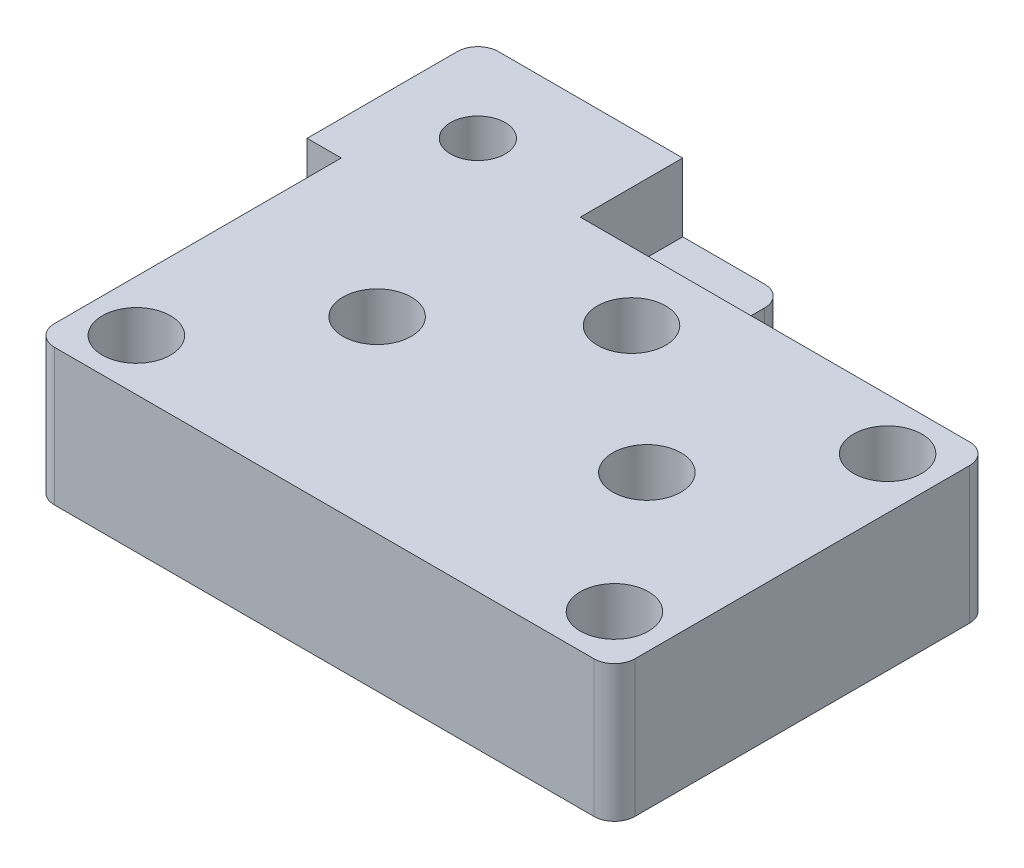
SolidWorks part; units mm, degrees
ref_plane "Alzado" through (0, 0, 0) normal (0, 0, 1) x (1, 0, 0)
ref_plane "Planta" through (0, 0, 0) normal (0, 1, 0) x (1, 0, 0)
ref_plane "Vista lateral" through (0, 0, 0) normal (1, 0, 0) x (0, 0, -1)
sketch "Croquis1" plane through (0, 0, 0) normal (0, 1, 0) x (1, 0, 0)
  line L0 (-2.5, 27.5) -> (-2.5, 42.5)
  line L1 (-42.5, -27.5) -> (42.5, -27.5)
  line L2 (-42.5, -27.5) -> (-42.5, 17.5)
  line L3 (-2.5, 27.5) -> (42.5, 27.5)
  line L4 (42.5, -27.5) -> (42.5, 27.5)
  line L5 (-42.5, -27.5) -> (42.5, 27.5) construction
  line L6 (0, 0) -> (42.5, -27.5) construction
  line L7 (-2.5, 42.5) -> (-47.5, 42.5)
  line L8 (-47.5, 42.5) -> (-47.5, 17.5)
  line L9 (-47.5, 17.5) -> (-42.5, 17.5)
  point P0 (0, 0)
  dimension "D1" = 85
  dimension "D2" = 55
  dimension "D3" = 5
  dimension "D4" = 25
  dimension "D5" = 45
  dimension "D6" = 15
  dimension "D7" = 27.5
extrude "Saliente-Extruir1" add sketch "Croquis1" along normal blind 20
sketch "Croquis2" plane through (0, 20, 0) normal (0, 1, 0) x (1, 0, 0)
  line L0 (-19.75, 0) -> (19.75, 0) construction
  line L1 (42.5, 20) -> (-35, 20) construction
  line L2 (42.5, -27.5) -> (42.5, 27.5) construction
  line L3 (-35, 20) -> (-35, -20) construction
  line L4 (-35, -20) -> (35, -20) construction
  line L5 (35, -20) -> (35, 20) construction
  line L6 (42.5, 27.5) -> (-2.5, 27.5) construction
  line L7 (-42.5, -27.5) -> (42.5, -27.5) construction
  line L8 (-42.5, 17.5) -> (-42.5, -27.5) construction
  line L9 (-2.5, 27.5) -> (-2.5, 42.5) construction
  line L10 (-2.5, 42.5) -> (-47.5, 42.5) construction
  circle A0 centre (-19.75, 0) radius 20 construction
  circle A1 centre (19.75, 0) radius 20 construction
  circle A2 centre (35, 20) radius 2.5
  circle A3 centre (35, -20) radius 2.5
  circle A4 centre (-35, -20) radius 2.5
  circle A5 centre (-10, 35) radius 2.5
  circle A7 centre (-19.75, 0) radius 5
  circle A8 centre (19.75, 0) radius 5
  point P5 (0, 0)
  dimension "D1" = 40
  dimension "D2" = 40
  dimension "D4" = 5
  dimension "D11" = 10
  dimension "D12" = 10
  dimension "D3" = 39.5
  dimension "D5" = 7.5
  dimension "D6" = 7.5
  dimension "D7" = 7.5
  dimension "D8" = 7.5
  dimension "D9" = 7.5
  dimension "D10" = 7.5
extrude "Cortar-Extruir1" cut sketch "Croquis2" against normal blind 20
sketch "Croquis3" plane through (0, 20, 0) normal (0, 1, 0) x (1, 0, 0)
  line L0 (-47.5, 42.5) -> (-47.5, 17.5) construction
  line L1 (-47.5, 17.5) -> (-42.5, 17.5) construction
  circle A0 centre (-35, 30) radius 4
  circle A1 centre (0, 17.5) radius 5
  circle A2 centre (-19.75, 0) radius 20 construction
  circle A3 centre (19.75, 0) radius 20 construction
  dimension "D1" = 10
  dimension "D2" = 8
  dimension "D6" = 40
  dimension "D7" = 40
  dimension "D3" = 12.5
  dimension "D4" = 12.5
  dimension "D5" = 17.5
extrude "Cortar-Extruir2" cut sketch "Croquis3" against normal blind 20
sketch "Croquis4" plane through (0, 0, 0) normal (0, -1, 0) x (1, 0, 0)
  line L0 (-28.2967, 4.8257) -> (11.25, 4.9075) construction
  line L1 (19.75, -9.815) -> (28.25, -4.9075)
  line L2 (28.25, -4.9075) -> (28.25, 4.9075)
  line L3 (28.25, 4.9075) -> (19.75, 9.815)
  line L4 (19.75, 9.815) -> (11.25, 4.9075)
  line L5 (11.25, 4.9075) -> (11.25, -4.9075)
  line L6 (11.25, -4.9075) -> (19.75, -9.815)
  line L7 (-19.6559, -9.8145) -> (-11.2033, -4.8257)
  line L8 (-11.2033, -4.8257) -> (-11.2975, 4.9888)
  line L9 (-11.2975, 4.9888) -> (-19.8441, 9.8145)
  line L10 (-19.8441, 9.8145) -> (-28.2967, 4.8257)
  line L11 (-28.2967, 4.8257) -> (-28.2025, -4.9888)
  line L12 (-28.2025, -4.9888) -> (-19.6559, -9.8145)
  line L13 (-35, -39.815) -> (-26.5, -34.9075)
  line L14 (-26.5, -34.9075) -> (-26.5, -25.0925)
  line L15 (-26.5, -25.0925) -> (-35, -20.185)
  line L16 (-35, -20.185) -> (-43.5, -25.0925)
  line L17 (-43.5, -25.0925) -> (-43.5, -34.9075)
  line L18 (-43.5, -34.9075) -> (-35, -39.815)
  circle A0 centre (19.75, 0) radius 8.5 construction
  circle A1 centre (-19.75, 0) radius 8.5 construction
  circle A2 centre (-35, -30) radius 8.5 construction
  point P19 (-11.2504, 0.0815)
  dimension "D1" = 17
  dimension "D2" = 17
  dimension "D3" = 17
  dimension "D4" = 39.5467
  dimension "D5" = 16.9992
extrude "Cortar-Extruir3" cut sketch "Croquis4" against normal blind 7.5
sketch "Croquis5" plane through (0, 20, 0) normal (0, 1, 0) x (1, 0, 0)
  line L0 (42.5, 27.5) -> (-2.5, 27.5) construction
  line L1 (-2.5, 42.5) -> (-17.5, 42.5)
  line L2 (-2.5, 42.5) -> (-2.5, 27.5)
  line L3 (-2.5, 27.5) -> (-17.5, 27.5)
  line L4 (-17.5, 42.5) -> (-17.5, 27.5)
  circle A0 centre (-35, -20) radius 5
  circle A1 centre (35, -20) radius 5
  circle A2 centre (35, 20) radius 5
  dimension "D1" = 10
  dimension "D2" = 15
extrude "Cortar-Extruir4" cut sketch "Croquis5" against normal blind 10
fillet "Redondeo1" radius 3 5 edges at (-47.5, 10, -42.5) (-2.5, 5, -42.5) (42.5, 10, -27.5) (42.5, 10, 27.5) (-42.5, 10, 27.5)
